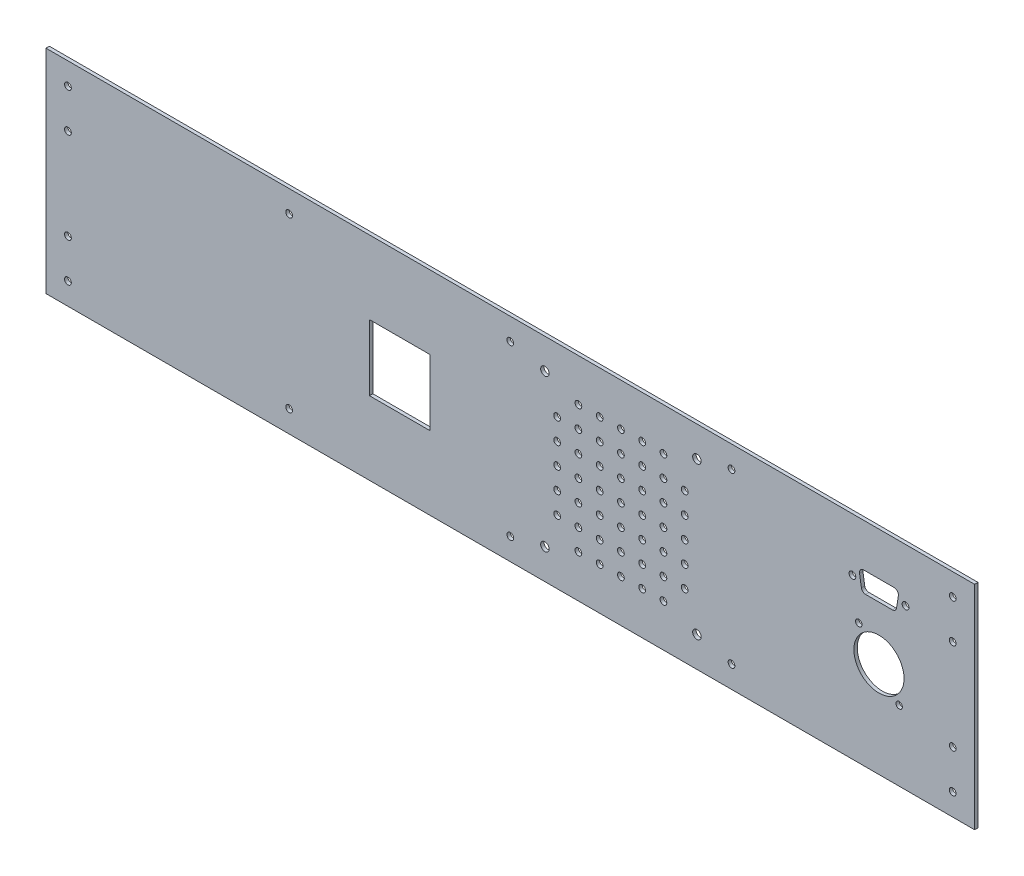
SolidWorks part; units mm, degrees
ref_plane "Plan de face" through (0, 0, 0) normal (0, 0, 1) x (1, 0, 0)
ref_plane "Plan de dessus" through (0, 0, 0) normal (0, 1, 0) x (1, 0, 0)
ref_plane "Plan de droite" through (0, 0, 0) normal (1, 0, 0) x (0, 0, -1)
sketch "Esquisse1" plane through (0, 0, 0) normal (0, 0, 1) x (1, 0, 0)
  line L1 (-120.1017, 81.1475) -> (316.7233, 81.1475)
  line L2 (-120.1017, 81.1475) -> (-120.1017, -18.8525)
  line L3 (-120.1017, -18.8525) -> (316.7233, -18.8525)
  line L4 (316.7233, 81.1475) -> (316.7233, -18.8525)
  dimension "D1" = 436.825
  dimension "D2" = 100
extrude "Boss.-Extru.1" add sketch "Esquisse1" along normal blind 1.5875
sketch "Esquisse2" plane through (0, 0, 0) normal (0, 0, -1) x (-1, 0, 0)
  line L0 (120.1017, -18.8525) -> (-316.7233, -18.8525) construction
  line L1 (-316.7233, -18.8525) -> (-316.7233, 81.1475) construction
  line L2 (-316.7233, 31.1475) -> (120.1017, 31.1475) construction
  line L3 (120.1017, 81.1475) -> (120.1017, -18.8525) construction
  line L4 (-306.4046, -8.5337) -> (-98.3108, -8.5337) construction
  line L5 (-98.3108, -8.5337) -> (109.7829, -8.5337) construction
  circle A1 centre (-306.4046, 9.7275) radius 1.5875
  circle A2 centre (-306.4046, -8.5337) radius 1.5875
  circle A3 centre (-98.3108, -8.5337) radius 1.5875
  circle A4 centre (-202.3577, -8.5337) radius 1.5875
  circle A5 centre (5.736, -8.5337) radius 1.5875
  circle A6 centre (109.7829, -8.5337) radius 1.5875
  circle A7 centre (109.7829, 9.7275) radius 1.5875
  circle A8 centre (109.7829, 52.5675) radius 1.5875
  circle A9 centre (109.7829, 70.8288) radius 1.5875
  circle A10 centre (5.736, 70.8288) radius 1.5875
  circle A11 centre (-98.3108, 70.8288) radius 1.5875
  circle A12 centre (-202.3577, 70.8288) radius 1.5875
  circle A13 centre (-306.4046, 70.8288) radius 1.5875
  circle A14 centre (-306.4046, 52.5675) radius 1.5875
  point P22 (-202.3577, -8.5337)
  point P23 (5.736, -8.5337)
  point P24 (-98.3108, -18.8525)
  dimension "D3" = 3.175
  dimension "D1" = 28.58
  dimension "D2" = 10.3187
  dimension "D4" = 10.3187
  dimension "D5" = 10.3187
extrude "Enlèv. mat.-Extru.1" cut sketch "Esquisse2" against normal up to next
sketch "Esquisse3" plane through (0, 0, 0) normal (0, 0, -1) x (-1, 0, 0)
  line L0 (-316.7233, -18.8525) -> (-316.7233, 81.1475) construction
  line L1 (-60.5374, 46.6475) -> (-32.0374, 46.6475)
  line L2 (-60.5374, 46.6475) -> (-60.5374, 15.6475)
  line L3 (-60.5374, 15.6475) -> (-32.0374, 15.6475)
  line L4 (-32.0374, 46.6475) -> (-32.0374, 15.6475)
  line L5 (-98.3108, 70.8288) -> (5.736, 70.8288) construction
  point P4 (-60.5374, 31.1475)
  point P7 (-316.7233, 31.1475)
  point P12 (-46.2874, 70.8288)
  point P13 (-46.2874, 46.6475)
  dimension "D1" = 28.5
  dimension "D2" = 31
extrude "Enlèv. mat.-Extru.2" cut sketch "Esquisse3" against normal up to next
sketch "Esquisse4" plane through (0, 0, 0) normal (0, 0, -1) x (-1, 0, 0)
  line L0 (-186.0843, 66.8975) -> (-186.0843, -4.6025) construction
  line L1 (-186.0843, -4.6025) -> (-114.5843, -4.6025) construction
  line L2 (-202.3577, -8.5337) -> (-98.3108, -8.5337) construction
  line L3 (-316.7233, -18.8525) -> (-316.7233, 81.1475) construction
  circle A0 centre (-186.0843, 66.8975) radius 2
  circle A1 centre (-114.5843, 66.8975) radius 2
  circle A2 centre (-114.5843, -4.6025) radius 2
  circle A3 centre (-186.0843, -4.6025) radius 2
  circle A4 centre (-150.3343, 31.1475) radius 1.5875
  circle A5 centre (-140.3343, 31.1475) radius 1.5875
  circle A6 centre (-130.3343, 31.1475) radius 1.5875
  circle A7 centre (-120.3343, 31.1475) radius 1.5875
  circle A8 centre (-140.3343, 41.1475) radius 1.5875
  circle A9 centre (-130.3343, 41.1475) radius 1.5875
  circle A10 centre (-120.3343, 41.1475) radius 1.5875
  circle A11 centre (-140.3343, 51.1475) radius 1.5875
  circle A12 centre (-130.3343, 51.1475) radius 1.5875
  circle A13 centre (-120.3343, 51.1475) radius 1.5875
  circle A14 centre (-140.3343, 61.1475) radius 1.5875
  circle A15 centre (-130.3343, 61.1475) radius 1.5875
  circle A20 centre (-160.3343, 31.1475) radius 1.5875
  circle A21 centre (-170.3343, 31.1475) radius 1.5875
  circle A22 centre (-180.3343, 31.1475) radius 1.5875
  circle A23 centre (-160.3343, 41.1475) radius 1.5875
  circle A24 centre (-170.3343, 41.1475) radius 1.5875
  circle A25 centre (-180.3343, 41.1475) radius 1.5875
  circle A26 centre (-160.3343, 51.1475) radius 1.5875
  circle A27 centre (-170.3343, 51.1475) radius 1.5875
  circle A28 centre (-180.3343, 51.1475) radius 1.5875
  circle A29 centre (-160.3343, 61.1475) radius 1.5875
  circle A30 centre (-170.3343, 61.1475) radius 1.5875
  circle A32 centre (-150.3343, 41.1475) radius 1.5875
  circle A33 centre (-150.3343, 51.1475) radius 1.5875
  circle A34 centre (-150.3343, 61.1475) radius 1.5875
  circle A35 centre (-180.3343, 61.1475) radius 1.5875 [skipped]
  circle A36 centre (-120.3343, 61.1475) radius 1.5875 [skipped]
  circle A37 centre (-150.3343, 21.1475) radius 1.5875
  circle A38 centre (-140.3343, 21.1475) radius 1.5875
  circle A39 centre (-130.3343, 21.1475) radius 1.5875
  circle A40 centre (-120.3343, 21.1475) radius 1.5875
  circle A41 centre (-140.3343, 11.1475) radius 1.5875
  circle A42 centre (-130.3343, 11.1475) radius 1.5875
  circle A43 centre (-120.3343, 11.1475) radius 1.5875
  circle A44 centre (-140.3343, 1.1475) radius 1.5875
  circle A45 centre (-130.3343, 1.1475) radius 1.5875
  circle A49 centre (-160.3343, 21.1475) radius 1.5875
  circle A50 centre (-170.3343, 21.1475) radius 1.5875
  circle A51 centre (-180.3343, 21.1475) radius 1.5875
  circle A52 centre (-160.3343, 11.1475) radius 1.5875
  circle A53 centre (-170.3343, 11.1475) radius 1.5875
  circle A54 centre (-180.3343, 11.1475) radius 1.5875
  circle A55 centre (-160.3343, 1.1475) radius 1.5875
  circle A56 centre (-170.3343, 1.1475) radius 1.5875
  circle A58 centre (-150.3343, 11.1475) radius 1.5875
  circle A59 centre (-150.3343, 1.1475) radius 1.5875
  circle A60 centre (-180.3343, 1.1475) radius 1.5875 [skipped]
  circle A61 centre (-120.3343, 1.1475) radius 1.5875 [skipped]
  circle A62 centre (-150.3343, 11.1475) radius 1.5875 [skipped]
  circle A63 centre (-150.3343, 1.1475) radius 1.5875 [skipped]
  circle A64 centre (-150.3343, 41.1475) radius 1.5875 [skipped]
  circle A65 centre (-150.3343, 51.1475) radius 1.5875 [skipped]
  circle A66 centre (-150.3343, 61.1475) radius 1.5875 [skipped]
  point P8 (-150.3343, -4.6025)
  point P11 (-150.3343, -8.5337)
  point P12 (-186.0843, 31.1475)
  point P17 (-316.7233, 31.1475)
  dimension "D1" = 4
  dimension "D3" = 3.175
  dimension "D2" = 71.5
  dimension "D4" = 4
  dimension "D5" = 4
  dimension "D6" = 4
  dimension "D7" = 4
  dimension "D8" = 2
  dimension "D12" = 4
  dimension "D9" = 3
  dimension "D11" = 4
  dimension "D10" = 3
extrude "Enlèv. mat.-Extru.3" cut sketch "Esquisse4" against normal up to next (1.5875 mm away)
sketch "Esquisse5" plane through (0, 0, 0) normal (0, 0, -1) x (-1, 0, 0)
  line L0 (-316.7233, -18.8525) -> (-316.7233, 81.1475) construction
  line L1 (-262.2233, 38.1475) -> (-262.2233, 14.1475) construction
  line L2 (-262.2233, 14.1475) -> (-281.2233, 14.1475) construction
  line L3 (120.1017, -18.8525) -> (-316.7233, -18.8525) construction
  line L4 (-259.2283, 56.1475) -> (-284.2183, 56.1475) construction
  line L5 (-316.7233, 81.1475) -> (120.1017, 81.1475) construction
  line L6 (-262.2233, 60.8975) -> (-281.2233, 60.8975)
  line L7 (-262.2233, 60.8975) -> (-263.7233, 51.3975)
  line L8 (-263.7233, 51.3975) -> (-279.7233, 51.3975)
  line L9 (-281.2233, 60.8975) -> (-279.7233, 51.3975)
  circle A0 centre (-271.7233, 26.1475) radius 11.8
  circle A1 centre (-262.2233, 38.1475) radius 1.5312
  circle A2 centre (-281.2233, 14.1475) radius 1.5312
  circle A3 centre (-259.2283, 56.1475) radius 1.5875
  circle A4 centre (-284.2183, 56.1475) radius 1.5875
  point P13 (-262.2233, 26.1475)
  point P15 (-271.7233, 14.1475)
  point P21 (-271.7233, 56.1475)
  point P26 (-271.7233, 60.8975)
  point P27 (-280.4733, 56.1475)
  point P31 (-271.7233, 51.3975)
  dimension "D1" = 23.6
  dimension "D2" = 3.0625
  dimension "D7" = 3.175
  dimension "D3" = 24
  dimension "D4" = 19
  dimension "D5" = 45
  dimension "D6" = 45
  dimension "D8" = 24.99
  dimension "D9" = 9.5
  dimension "D10" = 19
  dimension "D11" = 25
  dimension "D12" = 16
extrude "Enlèv. mat.-Extru.4" cut sketch "Esquisse5" against normal up to next
fillet "Congé1" radius 2 4 edges at (262.2233, 60.8975, 0.7937) (281.2233, 60.8975, 0.7937) (279.7233, 51.3975, 0.7937) (263.7233, 51.3975, 0.7937)
